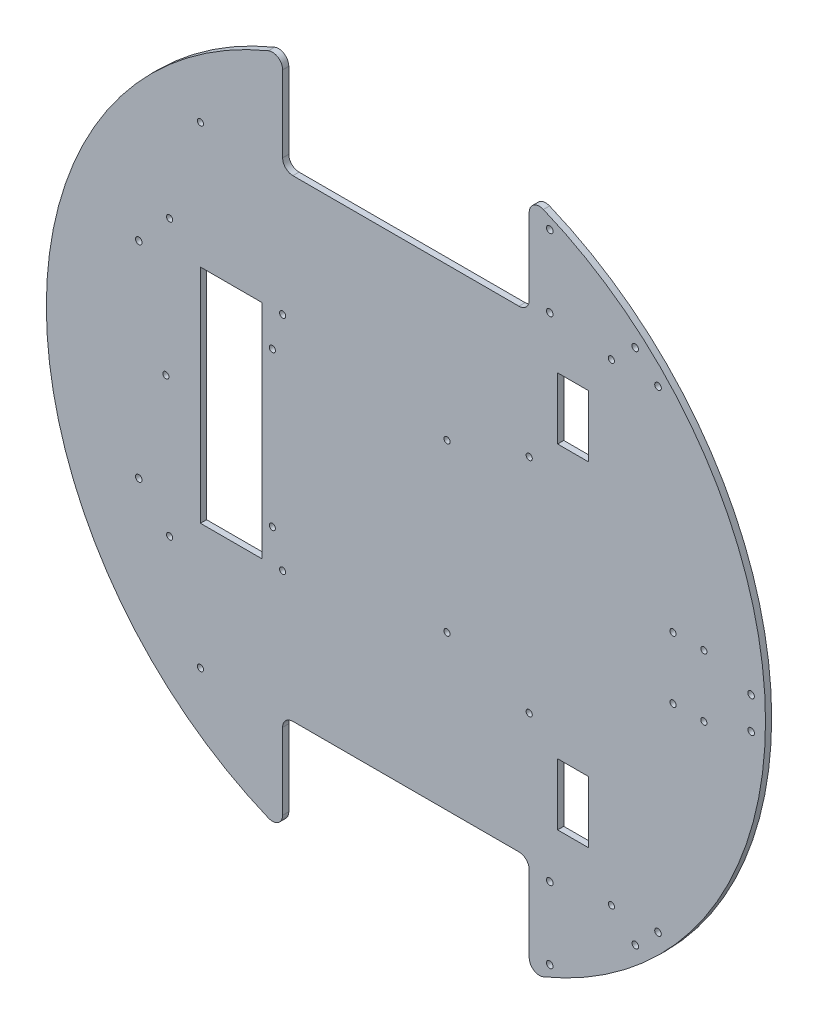
SolidWorks part; units mm, degrees
material "ｱｸﾘﾙ (中-上級の耐衝撃性)"
ref_plane "正面" through (0, 0, 0) normal (0, 0, 1) x (1, 0, 0)
ref_plane "平面" through (0, 0, 0) normal (0, 1, 0) x (1, 0, 0)
ref_plane "右側面" through (0, 0, 0) normal (1, 0, 0) x (0, 0, -1)
sketch "ｽｹｯﾁ1" plane through (0, 0, 0) normal (0, 0, 1) x (1, 0, 0)
  circle A0 centre (0, 0) radius 175
  dimension "D1" = 350
extrude "ﾎﾞｽ - 押し出し1" add sketch "ｽｹｯﾁ1" along normal blind 3
sketch "ｽｹｯﾁ2" plane through (0, 0, 3) normal (0, 0, 1) x (1, 0, 0)
  line L0 (0, 0) -> (175, 0)
  line L1 (0, 0) -> (-175, 0)
  line L2 (0, 0) -> (0, 115)
  line L3 (0, 0) -> (0, -115)
  line L4 (0, 115) -> (60, 115)
  line L5 (0, 115) -> (0, 175)
  line L6 (0, 175) -> (60, 175)
  line L7 (60, 115) -> (60, 175)
  line L8 (0, 115) -> (-60, 115)
  line L9 (0, 115) -> (0, 175)
  line L10 (0, 175) -> (-60, 175)
  line L11 (-60, 115) -> (-60, 175)
  line L13 (0, -115) -> (60, -115)
  line L14 (0, -115) -> (0, -175)
  line L15 (0, -175) -> (60, -175)
  line L16 (60, -115) -> (60, -175)
  line L17 (0, -115) -> (-60, -115)
  line L18 (0, -115) -> (0, -175)
  line L19 (0, -175) -> (-60, -175)
  line L20 (-60, -115) -> (-60, -175)
  circle A0 centre (0, 0) radius 175 construction
  circle M1 centre (0, 0) radius 175
  dimension "D1" = 115
  dimension "D2" = 60
  dimension "D3" = 60
  dimension "D4" = 60
  dimension "D5" = 115
  dimension "D6" = 60
extrude "ｶｯﾄ - 押し出し1" cut sketch "ｽｹｯﾁ2" against normal blind 3 contours L11 L8 L5 M1 | L4 L7 L5 M1 | L17 L20 L14 M1 | L16 L13 L14 M1
fillet "ﾌｨﾚｯﾄ1" radius 5 1 edges at (-60, 164.3928, 1.5)
fillet "ﾌｨﾚｯﾄ2" radius 5 3 edges at (60, 115, 1.5) (60, 164.3928, 1.5) (-60, 115, 1.5)
fillet "ﾌｨﾚｯﾄ3" radius 5 4 edges at (-60, -164.3928, 1.5) (-60, -115, 1.5) (60, -164.3928, 1.5) (60, -115, 1.5)
sketch "ｽｹｯﾁ5" plane through (0, 0, 3) normal (0, 0, 1) x (1, 0, 0)
  line L0 (0, 115) -> (-100, 115)
  line L1 (55, 115) -> (-55, 115) construction
  line L2 (0, 115) -> (100, 115)
  line L3 (0, -115) -> (100, -115)
  line L4 (55, -115) -> (-55, -115) construction
  line L5 (100, -115) -> (-100, -115)
  circle A0 centre (-100, -115) radius 1.5
  circle A1 centre (100, -115) radius 1.5
  circle A2 centre (100, 115) radius 1.5
  circle A3 centre (-100, 115) radius 1.5
  dimension "D3" = 3
  dimension "D4" = 3
  dimension "D5" = 3
  dimension "D6" = 3
  dimension "D1" = 100
  dimension "D2" = 100
extrude "ｶｯﾄ - 押し出し4" cut sketch "ｽｹｯﾁ5" against normal blind 3 contours A1 | A0 | A3 | A2
sketch "ｽｹｯﾁ6" plane through (0, 0, 3) normal (0, 0, 1) x (1, 0, 0)
  line L1 (-60, 54) -> (60, 54)
  line L2 (-60, 54) -> (-60, -54)
  line L3 (-60, -54) -> (60, -54)
  line L4 (60, 54) -> (60, -54)
  line L5 (-60, 54) -> (60, -54) construction
  line L6 (-60, -54) -> (60, 54) construction
  circle A0 centre (-60, 54) radius 1.5
  circle A1 centre (60, 54) radius 1.5
  circle A2 centre (-60, -54) radius 1.5
  circle A3 centre (60, -54) radius 1.5
  point P0 (0, 0)
  dimension "D3" = 3
  dimension "D4" = 3
  dimension "D5" = 3
  dimension "D6" = 3
  dimension "D1" = 120
  dimension "D2" = 108
extrude "ｶｯﾄ - 押し出し5" cut sketch "ｽｹｯﾁ6" against normal blind 3 contours A2 | A0 | A1 | A3
sketch "ｽｹｯﾁ7" plane through (0, 0, 3) normal (0, 0, 1) x (1, 0, 0)
  line L0 (-60, -54) -> (-70, -54)
  line L2 (-70, -54) -> (-100, -54)
  line L3 (-70, -54) -> (-70, 54)
  line L4 (-70, 54) -> (-100, 54)
  line L5 (-100, -54) -> (-100, 54)
  dimension "D1" = 10
  dimension "D2" = 108
  dimension "D3" = 30
extrude "ｶｯﾄ - 押し出し6" cut sketch "ｽｹｯﾁ7" against normal blind 3 contours L5 L2 L3 L4
sketch "ｽｹｯﾁ8" plane through (0, 0, 3) normal (0, 0, 1) x (1, 0, 0)
  line L0 (-100, 0) -> (-115, 0)
  line L1 (-100, -54) -> (-100, 54) construction
  line L2 (-115, 0) -> (-115, 67)
  line L3 (-115, 0) -> (-115, -67)
  circle A0 centre (-115, -67) radius 1.5
  circle A1 centre (-116.8225, 0) radius 1.5
  circle A2 centre (-115, 67) radius 1.5
  dimension "D4" = 3
  dimension "D5" = 3
  dimension "D6" = 3
  dimension "D1" = 15
  dimension "D2" = 67
  dimension "D3" = 67
extrude "ｶｯﾄ - 押し出し7" cut sketch "ｽｹｯﾁ8" against normal blind 3 contours A2 | A1 | A0
sketch "ｽｹｯﾁ9" plane through (0, 0, 3) normal (0, 0, 1) x (1, 0, 0)
  line L0 (-70, 0) -> (-65, 0)
  line L1 (-70, -54) -> (-70, 54) construction
  line L2 (-65, 0) -> (-65, 37)
  line L3 (-65, 37) -> (-64.7716, 37.1905)
  line L4 (-65, 0) -> (-65, -38)
  line L5 (-65, 0) -> (20, 0)
  line L6 (20, 0) -> (20, 41)
  line L7 (20, 0) -> (20, -40)
  circle A0 centre (-65, 37) radius 1.5
  circle A1 centre (20, 41) radius 1.5
  circle A2 centre (-65, -38) radius 1.5
  circle A3 centre (20, -40) radius 1.5
  dimension "D7" = 3
  dimension "D8" = 3
  dimension "D9" = 3
  dimension "D10" = 3
  dimension "D1" = 5
  dimension "D2" = 37
  dimension "D3" = 38
  dimension "D4" = 85
  dimension "D5" = 41
  dimension "D6" = 40
extrude "ｶｯﾄ - 押し出し8" cut sketch "ｽｹｯﾁ9" against normal blind 10 contours A0 | A2 | A1 | A3
sketch "ｽｹｯﾁ10" plane through (0, 0, 3) normal (0, 0, 1) x (1, 0, 0)
  line L0 (0, 0) -> (152.2366, 0)
  line L1 (0, 0) -> (66.9742, 68.8711)
  line L2 (0, 0) -> (76.2283, -78.3873)
  line L3 (175, 0) -> (168, 0)
  line L4 (-175, 0) -> (-168, 0)
  line L5 (66.9742, 68.8711) -> (117.1237, 120.441)
  line L6 (76.2283, -78.3873) -> (117.1237, -120.441)
  line L7 (117.1237, -120.441) -> (122.6798, -115.038)
  line L8 (117.1237, -120.441) -> (111.6437, -125.9211)
  line L9 (168, 0) -> (168, 7.75)
  line L10 (168, 0) -> (168, -7.75)
  line L11 (117.1237, 120.441) -> (111.5677, 125.844)
  line L12 (117.1237, 120.441) -> (122.6798, 115.038)
  arc A0 (66.9118, -161.7029) -> (66.9118, 161.7029) centre (0, 0) ccw construction
  arc A1 (-66.9118, 161.7029) -> (-66.9118, -161.7029) centre (0, 0) ccw construction
  circle A2 centre (0, 0) radius 168
  circle A3 centre (111.6437, -125.9211) radius 1.6
  circle A4 centre (122.6798, -115.038) radius 1.6
  circle A5 centre (168, 7.75) radius 1.6
  circle A6 centre (168, -7.75) radius 1.6
  circle A7 centre (111.5677, 125.844) radius 1.6
  circle A8 centre (122.6798, 115.038) radius 1.6
  dimension "D7" = 3.2
  dimension "D8" = 3.2
  dimension "D11" = 3.2
  dimension "D12" = 3.2
  dimension "D15" = 3.2
  dimension "D16" = 3.2
  dimension "D1" = 45.8
  dimension "D2" = 45.8
  dimension "D3" = 7
  dimension "D4" = 7
  dimension "D5" = 7.75
  dimension "D6" = 7.75
  dimension "D9" = 7.75
  dimension "D10" = 7.75
  dimension "D13" = 7.75
  dimension "D14" = 7.75
extrude "ｶｯﾄ - 押し出し9" cut sketch "ｽｹｯﾁ10" against normal blind 10 contours A3 | A4 | A6 | A5 | A7 | A8
sketch "ｽｹｯﾁ11" plane through (0, 0, 3) normal (0, 0, 1) x (1, 0, 0)
  line L0 (0, 0) -> (115, 0)
  line L1 (0, 0) -> (81.3173, 81.3173)
  line L2 (0, 0) -> (81.3173, -81.3173)
  line L4 (73.8173, 96.3173) -> (88.8173, 96.3173)
  line L5 (73.8173, 96.3173) -> (73.8173, 66.3173)
  line L6 (73.8173, 66.3173) -> (88.8173, 66.3173)
  line L7 (88.8173, 96.3173) -> (88.8173, 66.3173)
  line L8 (73.8173, 96.3173) -> (88.8173, 66.3173) construction
  line L9 (73.8173, 66.3173) -> (88.8173, 96.3173) construction
  line L10 (73.8173, -66.3173) -> (88.8173, -66.3173)
  line L11 (73.8173, -66.3173) -> (73.8173, -96.3173)
  line L12 (73.8173, -96.3173) -> (88.8173, -96.3173)
  line L13 (88.8173, -66.3173) -> (88.8173, -96.3173)
  line L14 (73.8173, -66.3173) -> (88.8173, -96.3173) construction
  line L15 (73.8173, -96.3173) -> (88.8173, -66.3173) construction
  circle A0 centre (0, 0) radius 115
  dimension "D1" = 230
  dimension "D2" = 45
  dimension "D3" = 45
  dimension "D4" = 30
  dimension "D5" = 15
  dimension "D6" = 15
  dimension "D7" = 30
extrude "ｶｯﾄ - 押し出し10" cut sketch "ｽｹｯﾁ11" against normal blind 10 contours L7 L6 L5 L4 | L13 L12 L11 L10
sketch "ｽｹｯﾁ13" plane through (0, 0, 3) normal (0, 0, 1) x (1, 0, 0)
  line L0 (-1000, 0) -> (49000, 0) construction
  line L1 (175, -1000) -> (175, 49000) construction
  line L2 (145, -1000) -> (145, 49000) construction
  line L3 (-885.4652, 15) -> (49114.5348, 15) construction
  line L4 (-880.5436, -15) -> (49119.4564, -15) construction
  line L5 (130, -1000) -> (130, 49000) construction
  arc A0 (66.9118, -161.7029) -> (66.9118, 161.7029) centre (0, 0) ccw construction
  circle A1 centre (130, 15) radius 1.5
  circle A2 centre (145, 15) radius 1.5
  circle A3 centre (130, -15) radius 1.5
  circle A4 centre (145, -15) radius 1.5
  point P9 (175, 0)
  dimension "D1" = 30
  dimension "D2" = 15
  dimension "D3" = 15
  dimension "D4" = 15
extrude "ｶｯﾄ - 押し出し12" cut sketch "ｽｹｯﾁ13" against normal through all
sketch "ｽｹｯﾁ14" plane through (0, 0, 3) normal (0, 0, 1) x (1, 0, 0)
  line L0 (70, -832.2472) -> (70, 49167.7528) construction
  line L1 (60, 120) -> (60, 157.0828) construction
  line L2 (-1000, 0) -> (49000, 0) construction
  line L3 (-950.4426, 120) -> (49049.5574, 120) construction
  line L4 (-935.9254, -120) -> (49064.0746, -120) construction
  line L5 (60, -1055.5) -> (60, 48944.5) construction
  line L6 (-60, -1055.5) -> (-60, 48944.5) construction
  line L7 (-1060, 54) -> (48940, 54) construction
  line L8 (-938.5, -54) -> (49061.5, -54) construction
  line L9 (-1171.4629, 50.05) -> (48828.5371, 50.05) construction
  line L10 (-1151.5242, -50.05) -> (48848.4758, -50.05) construction
  line L11 (-130, -938.9506) -> (-130, 49061.0494) construction
  circle A0 centre (70, 119.7921) radius 1.6
  circle A1 centre (70, 154.7921) radius 1.6
  circle A2 centre (70, -120) radius 1.6
  circle A3 centre (70, -155) radius 1.6
  circle A4 centre (-130, 50.05) radius 1.6
  circle A5 centre (-130, -50.05) radius 1.6
  arc A6 (-66.9118, 161.7029) -> (-66.9118, -161.7029) centre (0, 0) ccw construction
  dimension "D4" = 3.2
  dimension "D5" = 3.2
  dimension "D7" = 3.2
  dimension "D8" = 3.2
  dimension "D10" = 50.05
  dimension "D12" = 3.2
  dimension "D13" = 3.2
  dimension "D1" = 10
  dimension "D2" = 120
  dimension "D3" = 120
  dimension "D6" = 35
  dimension "D9" = 35
  dimension "D11" = 50.05
  dimension "D14" = 130
extrude "ｶｯﾄ - 押し出し14" cut sketch "ｽｹｯﾁ14" against normal through all
